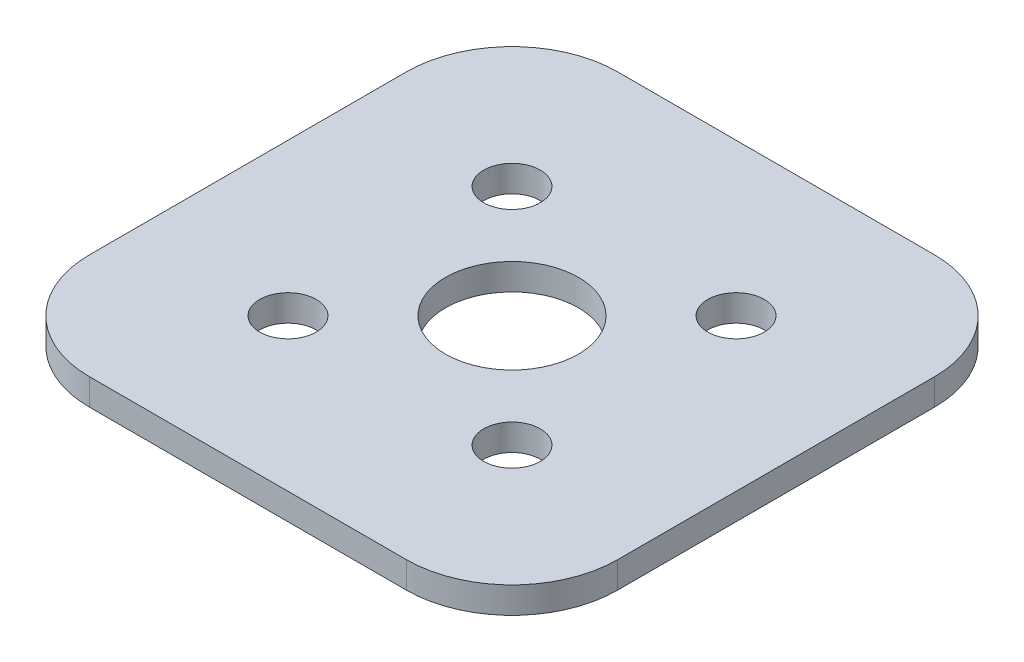
SolidWorks part; units mm, degrees
ref_plane "Front Plane" through (0, 0, 0) normal (0, 0, 1) x (1, 0, 0)
ref_plane "Top Plane" through (0, 0, 0) normal (0, 1, 0) x (1, 0, 0)
ref_plane "Right Plane" through (0, 0, 0) normal (1, 0, 0) x (0, 0, -1)
sketch "Sketch1" plane through (0, 0, 0) normal (0, 1, 0) x (1, 0, 0)
  line L0 (-6.7352, 6.7352) -> (6.7352, -6.7352) construction
  line L2 (-6.7352, -6.7352) -> (6.7352, 6.7352) construction
  line L5 (-9.525, 15.875) -> (9.525, 15.875)
  line L6 (-15.875, 9.525) -> (-15.875, -9.525)
  line L7 (-9.525, -15.875) -> (9.525, -15.875)
  line L8 (15.875, 9.525) -> (15.875, -9.525)
  line L9 (-15.875, 15.875) -> (15.875, -15.875) construction
  line L10 (-15.875, -15.875) -> (15.875, 15.875) construction
  circle A0 centre (-6.7352, -6.7352) radius 1.7
  circle A1 centre (6.7352, -6.7352) radius 1.7
  circle A2 centre (0, 0) radius 4
  circle A3 centre (6.7352, 6.7352) radius 1.7
  circle A4 centre (-6.7352, 6.7352) radius 1.7
  arc A5 (-15.875, 9.525) -> (-9.525, 15.875) centre (-9.525, 9.525) cw
  arc A6 (-9.525, -15.875) -> (-15.875, -9.525) centre (-9.525, -9.525) cw
  arc A7 (9.525, -15.875) -> (15.875, -9.525) centre (9.525, -9.525) ccw
  arc A8 (9.525, 15.875) -> (15.875, 9.525) centre (9.525, 9.525) cw
  dimension "D1" = 8
  dimension "D2" = 3.4
  dimension "D12" = 6.35
  dimension "D13" = 6.35
  dimension "D14" = 6.35
  dimension "D15" = 6.35
  dimension "D3" = 13.4704
  dimension "D4" = 13.4704
  dimension "D5" = 9.525
  dimension "D6" = 13.4704
  dimension "D7" = 9.525
  dimension "D8" = 9.525
  dimension "D9" = 9.525
  dimension "D10" = 31.75
  dimension "D11" = 31.75
extrude "Boss-Extrude1" add sketch "Sketch1" along normal blind 1.5875
equation "\"Aluminum_Screwhole_Diameter\"=0.133858"
equation "\"D2@Sketch1\"=\"Aluminum_Screwhole_Diameter\""
